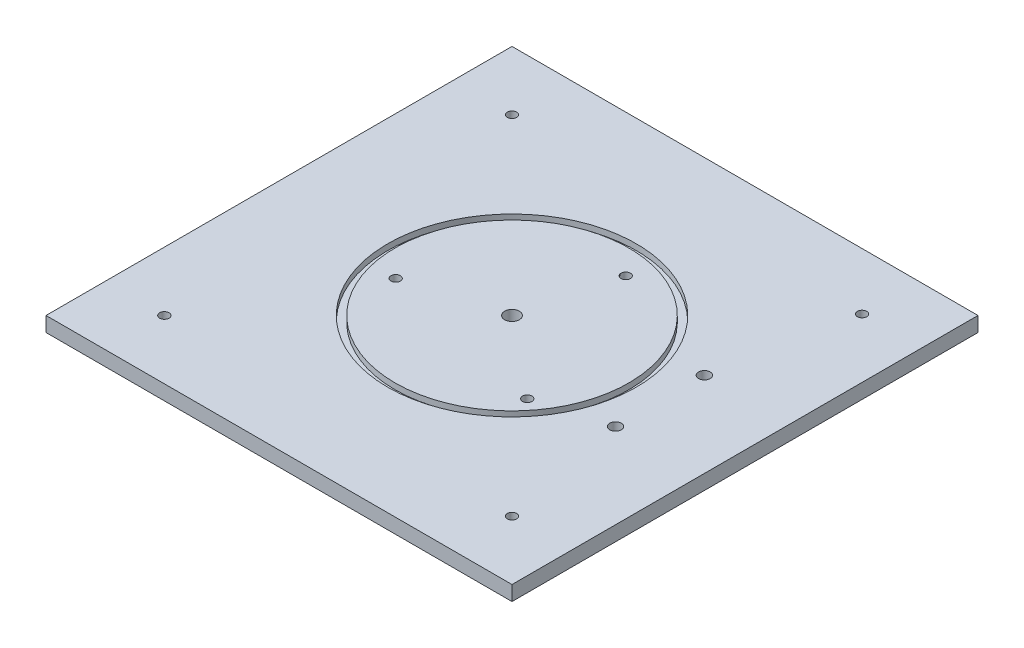
SolidWorks part; units mm, degrees
ref_plane "Front Plane" through (0, 0, 0) normal (0, 0, 1) x (1, 0, 0)
ref_plane "Top Plane" through (0, 0, 0) normal (0, 1, 0) x (1, 0, 0)
ref_plane "Right Plane" through (0, 0, 0) normal (1, 0, 0) x (0, 0, -1)
sketch "Sketch1" plane through (0, 0, 0) normal (0, 1, 0) x (1, 0, 0)
  line L1 (-100, 100) -> (100, 100)
  line L2 (-100, 100) -> (-100, -100)
  line L3 (-100, -100) -> (100, -100)
  line L4 (100, 100) -> (100, -100)
  line L5 (-100, 100) -> (100, -100) construction
  line L6 (-100, -100) -> (100, 100) construction
  point P0 (0, 0)
  dimension "D1" = 200
  dimension "D2" = 200
extrude "Boss-Extrude1" add sketch "Sketch1" along normal blind 6.35
sketch "Sketch2" plane through (0, 6.35, 0) normal (0, 1, 0) x (1, 0, 0)
  line L0 (-100, -100) -> (100, 100) construction
  line L1 (-100, -100) -> (100, -100) construction
  line L2 (-100, 100) -> (-100, -100) construction
  circle A0 centre (0, 0) radius 3.175
  point P5 (0, 0)
  dimension "D1" = 6.35
extrude "Cut-Extrude1" cut sketch "Sketch2" against normal through all
sketch "Sketch3" plane through (0, 6.35, 0) normal (0, 1, 0) x (1, 0, 0)
  line L0 (68.2625, 34.29) -> (68.2625, -34.29) construction
  line L1 (49.2125, 34.29) -> (68.2625, 34.29) construction
  line L2 (68.2625, -34.29) -> (49.2125, -34.29) construction
  circle A0 centre (63.5, -19.05) radius 2.4892
  circle A1 centre (63.5, 19.05) radius 2.4892
  dimension "D1" = 4.7625
  dimension "D2" = 4.7625
  dimension "D3" = 15.24
  dimension "D4" = 15.24
  dimension "D5" = 4.9784
  dimension "D6" = 4.9784
extrude "Cut-Extrude2" cut sketch "Sketch3" against normal through all
sketch "Sketch4" plane through (0, 6.35, 0) normal (0, 1, 0) x (1, 0, 0)
  circle A0 centre (0, 0) radius 50.165
  circle A1 centre (0, 0) radius 53.34
  dimension "D1" = 3.175
extrude "Cut-Extrude3" cut sketch "Sketch4" against normal blind 2.54
hole_wizard "#10-32 Tapped Hole1" positions "Sketch8" profile "Sketch7" tap size "#10-32" standard "ANSI Inch"
sketch "Sketch8" plane through (0, 6.35, 0) normal (0, 1, 0) x (1, 0, 0)
  circle A1 centre (0, 0) radius 3.175 construction
  point P0 (9.6933, 39.1401)
  point P3 (-38.7429, -11.1754)
  point P6 (34.2256, -27.6831)
  dimension "D2" = 44.0199
  dimension "D3" = 40.3225
  dimension "D1" = 40.3225
  dimension "D4" = 74.8126
  dimension "D5" = 69.8406
sketch "Sketch7" plane through (9.6933, 6.35, -39.1401) normal (1, 0, 0) x (0, 0, 1)
  line L0 (0, 0) -> (0, 14.9293)
  line L1 (0, 14.9293) -> (2.0193, 13.716)
  line L2 (2.0193, 13.716) -> (2.0193, 0)
  line L5 (2.0193, 0) -> (0, 0)
  line L10 (0, 14.9293) -> (-2.0193, 13.716) construction
  line L11 (0, -6.35) -> (0, 107.95) construction
  dimension "Tap Drill Dia." = 4.0386
  dimension "Tap Drill Depth" = 13.716
  dimension "Drill Angle" = 118
cosmetic thread "Hole Thread1" parameters "D1"=6.35, "D2"=4.826
cosmetic thread "Hole Thread2" parameters "D1"=6.35, "D2"=4.826
cosmetic thread "Hole Thread3" parameters "D1"=6.35, "D2"=4.826
sketch "Sketch9" plane through (0, 6.35, 0) normal (0, 1, 0) x (1, 0, 0)
  line L0 (100, 100) -> (-100, 100) construction
  line L1 (-100, 100) -> (-100, -100) construction
  line L2 (100, -100) -> (100, 100) construction
  line L3 (-100, -100) -> (100, -100) construction
  circle A0 centre (-74.6, 74.6) radius 2.02
  circle A1 centre (74.6, 75.6606) radius 2.02
  circle A2 centre (74.6, -74.6) radius 2.02
  circle A3 centre (-74.6, -74.6) radius 2.032
  dimension "D1" = 4.04
  dimension "D3" = 25.4
  dimension "D5" = 4.04
  dimension "D6" = 4.04
  dimension "D8" = 4.064
  dimension "D2" = 25.4
  dimension "D4" = 25.4
  dimension "D7" = 25.4
extrude "Cut-Extrude4" cut sketch "Sketch9" against normal through all
